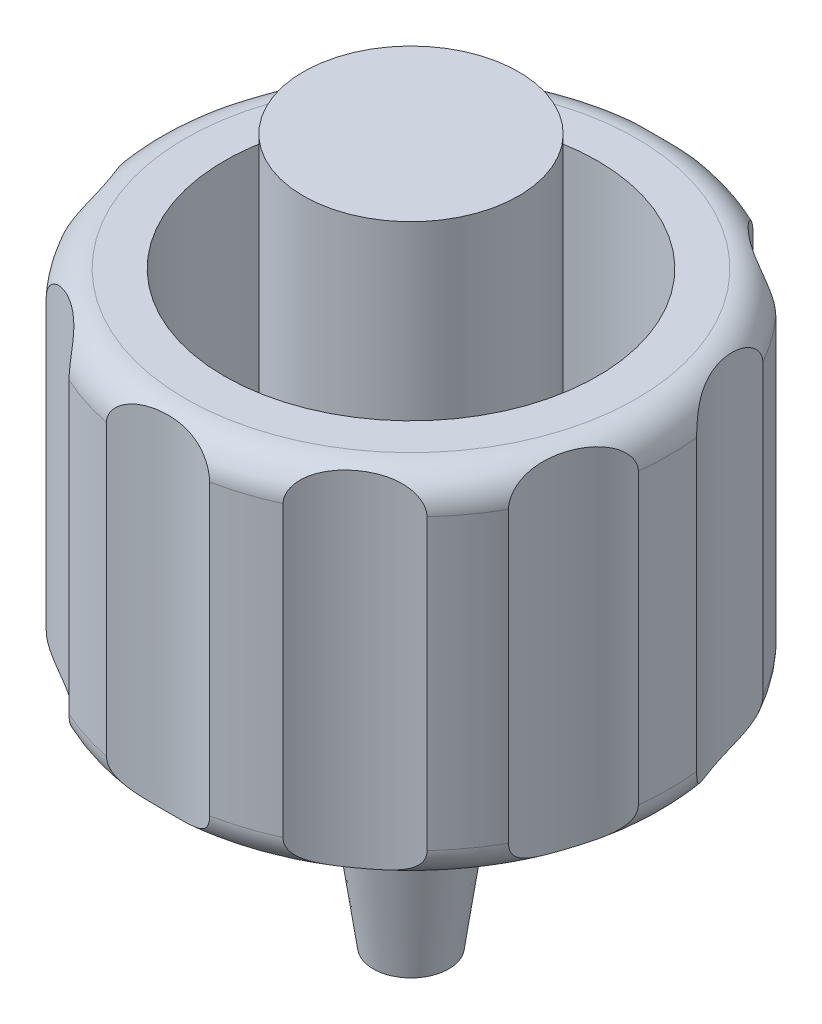
SolidWorks part; units mm, degrees
ref_plane "Front Plane" through (0, 0, 0) normal (0, 0, 1) x (1, 0, 0)
ref_plane "Top Plane" through (0, 0, 0) normal (0, 1, 0) x (1, 0, 0)
ref_plane "Right Plane" through (0, 0, 0) normal (1, 0, 0) x (0, 0, -1)
sketch "Sketch1" plane through (0, 0, 0) normal (0, 1, 0) x (1, 0, 0)
  circle A0 centre (0, 0) radius 5.535
  dimension "D1" = 11.07
extrude "Boss-Extrude1" add sketch "Sketch1" along normal blind 7.6
fillet "Fillet1" radius 0.7 2 edges at (0, 7.6, 5.535) (0, 0, 5.535)
sketch "Sketch2" plane through (0, 0, 0) normal (0, -1, 0) x (-1, 0, 0)
  line L0 (0, 0) -> (0, 8.2125) construction
  circle A0 centre (0, 8.2125) radius 3
  dimension "D1" = 6
extrude "Cut-Extrude1" cut sketch "Sketch2" against normal blind 7.6
pattern_circular "CirPattern1" count 10 over 360 about axis through (0, 0, 0) along (0, 1, 0) of "Cut-Extrude1"
sketch "Sketch3" plane through (0, 0, 0) normal (0, 0, 1) x (1, 0, 0)
  line L0 (1.15, 0) -> (1, -1.2)
  line L1 (1, -1.2) -> (1, -2.58)
  line L2 (1, -2.58) -> (1.15, -2.58)
  line L3 (1.15, -2.58) -> (0.81, -5)
  line L4 (0.81, -5) -> (0, -5)
  line L5 (0, -5) -> (0, 0)
  line L6 (0, 0) -> (1.15, 0)
  dimension "D1" = 1
  dimension "D2" = 1.15
  dimension "D3" = 1.2
  dimension "D4" = 5
  dimension "D5" = 2.42
  dimension "D6" = 1.15
  dimension "D7" = 0.81
revolve "Revolve1" add sketch "Sketch3" angle 360 about L5
sketch "Sketch4" plane through (0, 7.6, 0) normal (0, 1, 0) x (1, 0, 0)
  circle A0 centre (0, 0) radius 4
  dimension "D1" = 8
extrude "Cut-Extrude2" cut sketch "Sketch4" against normal blind 6.4
sketch "Sketch5" plane through (0, 1.2, 0) normal (0, 1, 0) x (1, 0, 0)
  circle A0 centre (0, 0) radius 2.3078
extrude "Boss-Extrude2" add sketch "Sketch5" along normal blind 8.9
